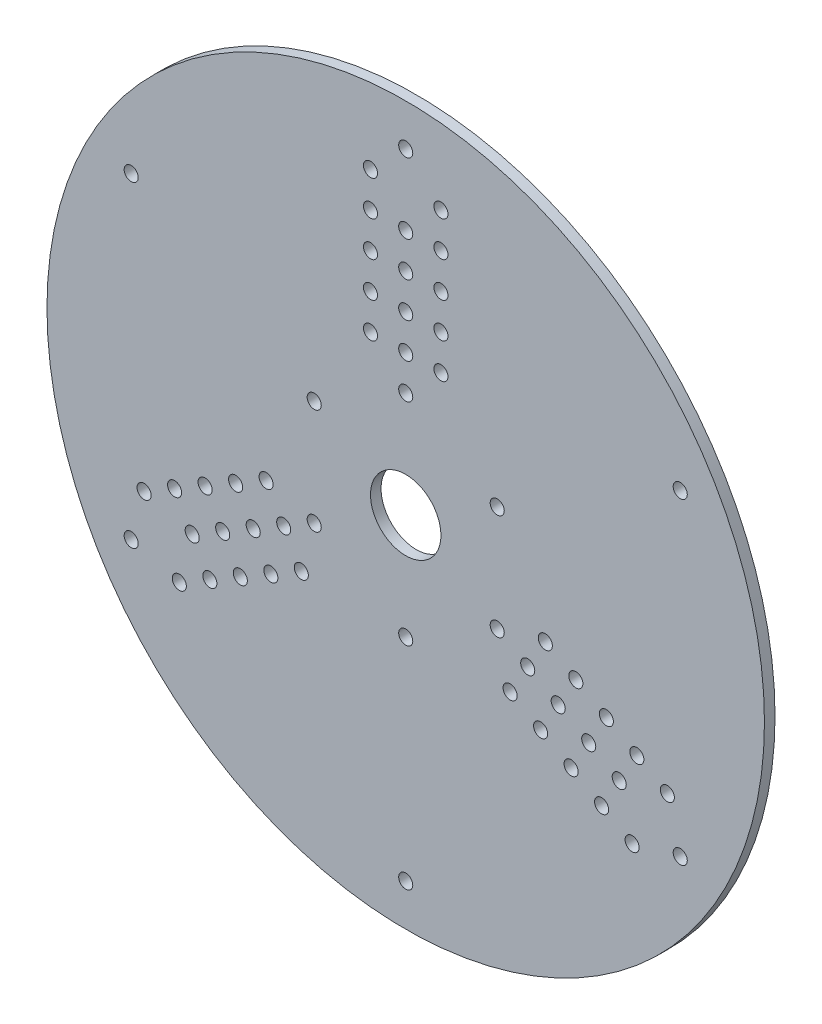
SolidWorks part; units mm, degrees
ref_plane "Front Plane" through (0, 0, 0) normal (0, 0, 1) x (1, 0, 0)
ref_plane "Top Plane" through (0, 0, 0) normal (0, 1, 0) x (1, 0, 0)
ref_plane "Right Plane" through (0, 0, 0) normal (1, 0, 0) x (0, 0, -1)
sketch "Sketch1" plane through (0, 0, 0) normal (0, 0, 1) x (1, 0, 0)
  circle A0 centre (0, 0) radius 101.8592
  circle A1 centre (0, 30) radius 2
  circle A2 centre (-10, 50) radius 2
  circle A3 centre (0, 40) radius 2
  circle A4 centre (10, 50) radius 2
  circle A5 centre (-10, 60) radius 2
  circle A6 centre (-10, 40) radius 2
  circle A7 centre (10, 40) radius 2
  circle A8 centre (0, 50) radius 2
  circle A9 centre (10, 60) radius 2
  circle A10 centre (-10, 70) radius 2
  circle A11 centre (0, 60) radius 2
  circle A12 centre (10, 70) radius 2
  circle A13 centre (-10, 80) radius 2
  circle A14 centre (0, 70) radius 2
  circle A15 centre (10, 80) radius 2
  circle A16 centre (25.9808, -15) radius 2
  circle A17 centre (48.3013, -16.3397) radius 2
  circle A18 centre (34.641, -20) radius 2
  circle A19 centre (38.3013, -33.6603) radius 2
  circle A20 centre (56.9615, -21.3397) radius 2
  circle A21 centre (39.641, -11.3397) radius 2
  circle A22 centre (29.641, -28.6603) radius 2
  circle A23 centre (43.3013, -25) radius 2
  circle A24 centre (46.9615, -38.6603) radius 2
  circle A25 centre (65.6218, -26.3397) radius 2
  circle A26 centre (51.9615, -30) radius 2
  circle A27 centre (55.6218, -43.6603) radius 2
  circle A28 centre (74.282, -31.3397) radius 2
  circle A29 centre (60.6218, -35) radius 2
  circle A30 centre (64.282, -48.6603) radius 2
  circle A31 centre (-25.9808, -15) radius 2
  circle A32 centre (-38.3013, -33.6603) radius 2
  circle A33 centre (-34.641, -20) radius 2
  circle A34 centre (-48.3013, -16.3397) radius 2
  circle A35 centre (-46.9615, -38.6603) radius 2
  circle A36 centre (-29.641, -28.6603) radius 2
  circle A37 centre (-39.641, -11.3397) radius 2
  circle A38 centre (-43.3013, -25) radius 2
  circle A39 centre (-56.9615, -21.3397) radius 2
  circle A40 centre (-55.6218, -43.6603) radius 2
  circle A41 centre (-51.9615, -30) radius 2
  circle A42 centre (-65.6218, -26.3397) radius 2
  circle A43 centre (-64.282, -48.6603) radius 2
  circle A44 centre (-60.6218, -35) radius 2
  circle A45 centre (-74.282, -31.3397) radius 2
  circle A46 centre (77.9423, 45) radius 2
  circle A47 centre (77.9423, -45) radius 2
  circle A48 centre (0, -90) radius 2
  circle A49 centre (-77.9423, -45) radius 2
  circle A50 centre (-77.9423, 45) radius 2
  circle A51 centre (0, 90) radius 2
  circle A52 centre (0, 0) radius 10
  circle A53 centre (25.9808, 15) radius 2
  circle A54 centre (0, -30) radius 2
  circle A55 centre (-25.9808, 15) radius 2
  point P96 (0, 0)
  point P109 (0, 0)
  point P117 (0, 0)
  dimension "D1" = 203.7183
  dimension "D3" = 4
  dimension "D5" = 4
  dimension "D6" = 4
  dimension "D8" = 4
  dimension "D12" = 20
  dimension "D13" = 4
  dimension "D2" = 30
  dimension "D4" = 5
  dimension "D9" = 90
  dimension "D10" = 60
  dimension "D14" = 60
  dimension "D15" = 30
  dimension "D17" = 10
  dimension "D18" = 10
  dimension "D7" = 3
  dimension "D11" = 6
  dimension "D16" = 3
extrude "Boss-Extrude1" add sketch "Sketch1" along normal blind 3
